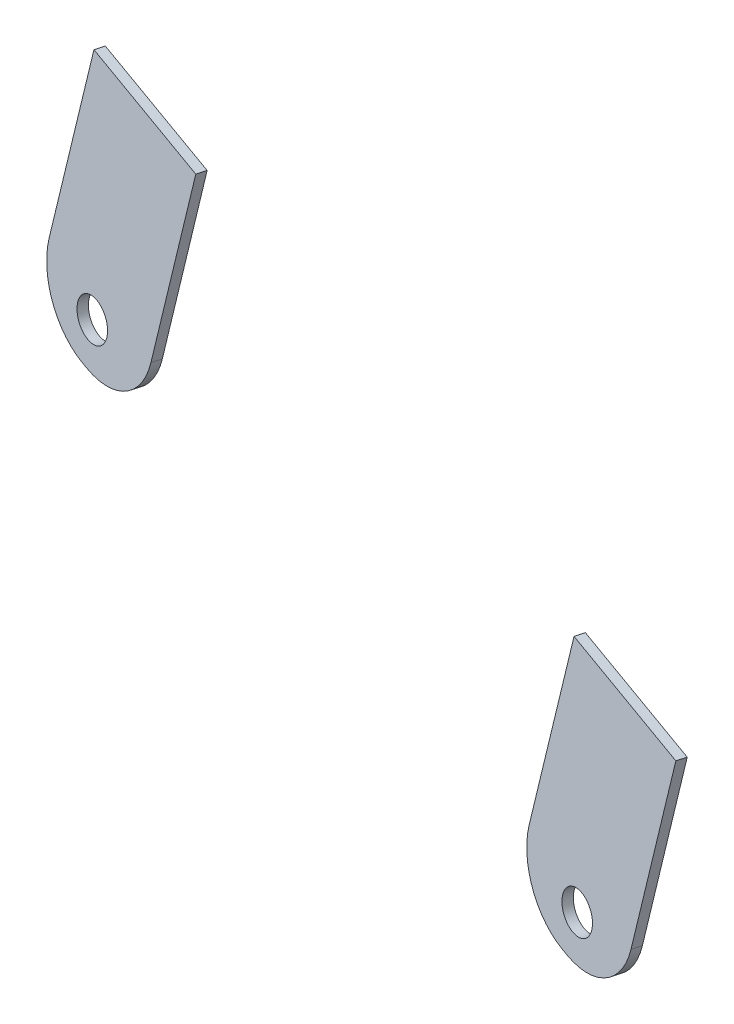
SolidWorks part; units mm, degrees
material "Stal węglowa"
ref_plane "Płaszczyzna XY" through (0, 0, 0) normal (0, 0, 1) x (1, 0, 0)
ref_plane "Płaszczyzna XZ" through (0, 0, 0) normal (0, 1, 0) x (1, 0, 0)
ref_plane "Płaszczyzna YZ" through (0, 0, 0) normal (1, 0, 0) x (0, 0, -1)
sketch3d "Szkic 3D4"
  line L0 (1025.706, -216.289, 105.3187) -> (1045.7616, -220.8039, 109.607)
  line L1 (1045.7616, -220.8039, 109.607) -> (1042.1945, -236.3989, 109.8707)
  line L2 (1025.706, -216.289, 105.3187) -> (1022.1389, -231.884, 105.5823)
  line L3 (1029.4597, -243.7809, 107.7892) -> (1030.4147, -243.9959, 107.9934)
  line L4 (1120.2537, -237.5736, 125.535) -> (1140.3093, -242.0885, 129.8234)
  line L5 (1140.3093, -242.0885, 129.8234) -> (1136.7421, -257.6836, 130.0871)
  line L6 (1120.2537, -237.5736, 125.535) -> (1116.6866, -253.1687, 125.7987)
  line L7 (1124.0074, -265.0655, 128.0056) -> (1124.9624, -265.2805, 128.2098)
  arc A0 (1022.1389, -231.884, 105.5823) -> (1029.4597, -243.7809, 107.7892) centre (1031.6892, -234.034, 107.6244) ccw
  arc A2 (1030.4147, -243.9959, 107.9934) -> (1042.1945, -236.3989, 109.8707) centre (1032.6442, -234.249, 107.8286) ccw
  circle A4 centre (1030.9231, -237.3829, 107.681) radius 3
  arc A6 (1116.6866, -253.1687, 125.7987) -> (1124.0074, -265.0655, 128.0056) centre (1126.2368, -255.3186, 127.8408) ccw
  arc A8 (1124.9624, -265.2805, 128.2098) -> (1136.7421, -257.6836, 130.0871) centre (1127.1919, -255.5336, 128.045) ccw
  circle A10 centre (1126.4258, -258.8825, 128.1016) radius 3
  point P10 (1029.7342, -233.4213, 117.4123)
  point P17 (1030.6892, -233.6363, 117.6165)
  point P24 (1030.3367, -237.1991, 110.6174)
  point P40 (1124.2819, -254.706, 137.6287)
  point P47 (1125.2369, -254.921, 137.8329)
  point P56 (1125.8394, -258.6987, 131.038)
sketch3d "Szkic 3D5"
  line L0 (1140.3093, -242.0885, 129.8234) -> (1140.6025, -242.1804, 128.3552)
  line L1 (1120.2537, -237.5736, 125.535) -> (1140.3093, -242.0885, 129.8234) construction
  line L2 (1140.3093, -242.0885, 129.8234) -> (1136.7421, -257.6836, 130.0871) construction
  dimension "D1" = 1.5
extrude "Dodanie-wyciągnięcie2" add sketch "Szkic 3D4" along direction (0.1955, -0.0613, -0.9788) on the side against the normal blind 1.5
sketch "Szkic1" plane through (3.5956, 15.7194, -0.2658) normal (0.2229, 0.9747, -0.0165) x (0.9748, -0.2229, 0.0038)
  line L4 (1145.1886, -122.9704) -> (1165.762, -127.1818)
  line L5 (1165.762, -127.1818) -> (1166.0628, -125.7122)
  line L6 (1166.0628, -125.7122) -> (1145.4894, -121.5009)
  line L7 (1145.4894, -121.5009) -> (1145.1886, -122.9704)
  line L8 (1145.1886, -122.9704) -> (1165.762, -127.1818)
  line L9 (1165.762, -127.1818) -> (1166.0628, -125.7122)
  line L10 (1166.0628, -125.7122) -> (1145.4894, -121.5009)
  line L11 (1145.4894, -121.5009) -> (1145.1886, -122.9704)
  line L12 (1048.1998, -103.1167) -> (1068.7732, -107.3281)
  line L13 (1068.7732, -107.3281) -> (1069.074, -105.8586)
  line L14 (1069.074, -105.8586) -> (1048.5006, -101.6472)
  line L15 (1048.5006, -101.6472) -> (1048.1998, -103.1167)
  line L16 (1048.1998, -103.1167) -> (1068.7732, -107.3281)
  line L17 (1068.7732, -107.3281) -> (1069.074, -105.8586)
  line L18 (1069.074, -105.8586) -> (1048.5006, -101.6472)
  line L19 (1048.5006, -101.6472) -> (1048.1998, -103.1167)
  dimension "D1" = 0
  dimension "D2" = 0
extrude "Dodanie-wyciągnięcie3" add sketch "Szkic1" along normal blind 13
